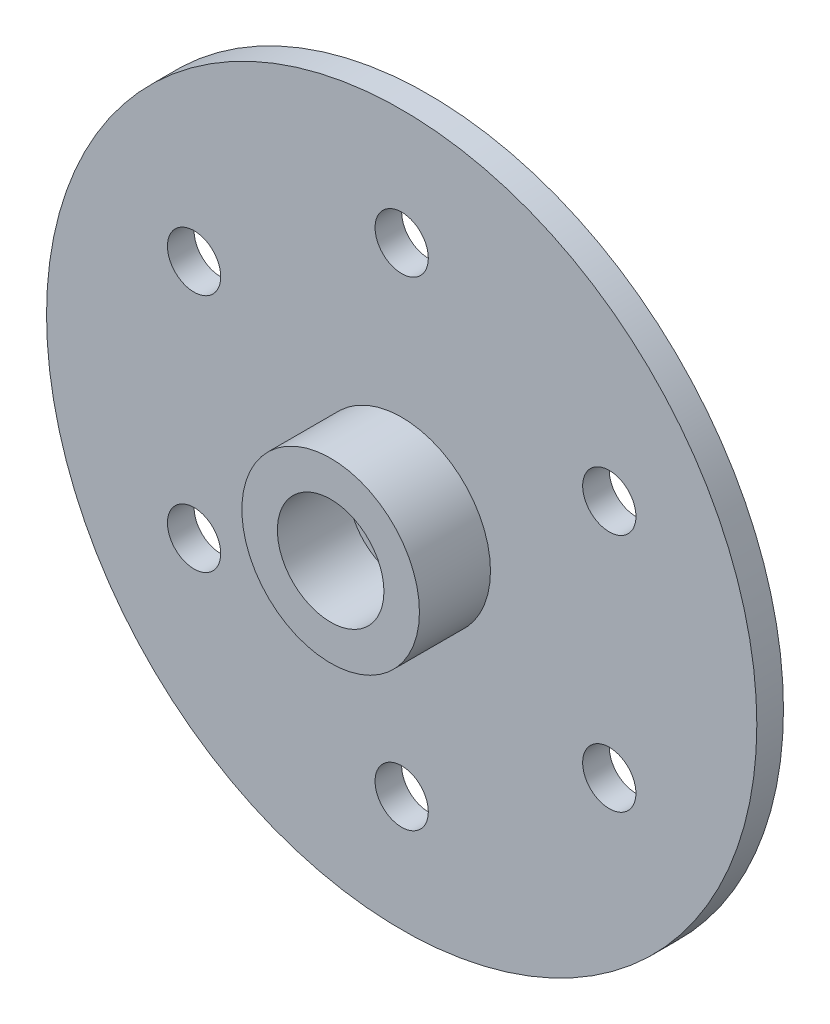
SolidWorks part; units mm, degrees
ref_plane "Front Plane" through (0, 0, 0) normal (0, 0, 1) x (1, 0, 0)
ref_plane "Top Plane" through (0, 0, 0) normal (0, 1, 0) x (1, 0, 0)
ref_plane "Right Plane" through (0, 0, 0) normal (1, 0, 0) x (0, 0, -1)
sketch "Sketch1" plane through (0, 0, 0) normal (0, 0, 1) x (1, 0, 0)
  circle A0 centre (-34.2487, 70.7944) radius 20
  circle A1 centre (-45.9401, 77.5444) radius 1.5
  circle A2 centre (-34.2487, 84.2944) radius 1.5
  circle A3 centre (-22.5574, 77.5444) radius 1.5
  circle A4 centre (-22.5574, 64.0444) radius 1.5
  circle A5 centre (-34.2487, 57.2944) radius 1.5
  circle A6 centre (-45.9401, 64.0444) radius 1.5
  circle A7 centre (-34.2487, 70.7944) radius 1
extrude "Boss-Extrude1" add sketch "Sketch1" along normal blind 1.5
sketch "Sketch2" plane through (0, 0, 1.5) normal (0, 0, 1) x (1, 0, 0)
  circle A0 centre (-34.2487, 70.7944) radius 3
  circle A1 centre (-34.2487, 70.7944) radius 5
  dimension "D1" = 10
extrude "Boss-Extrude2" add sketch "Sketch2" along normal blind 4
